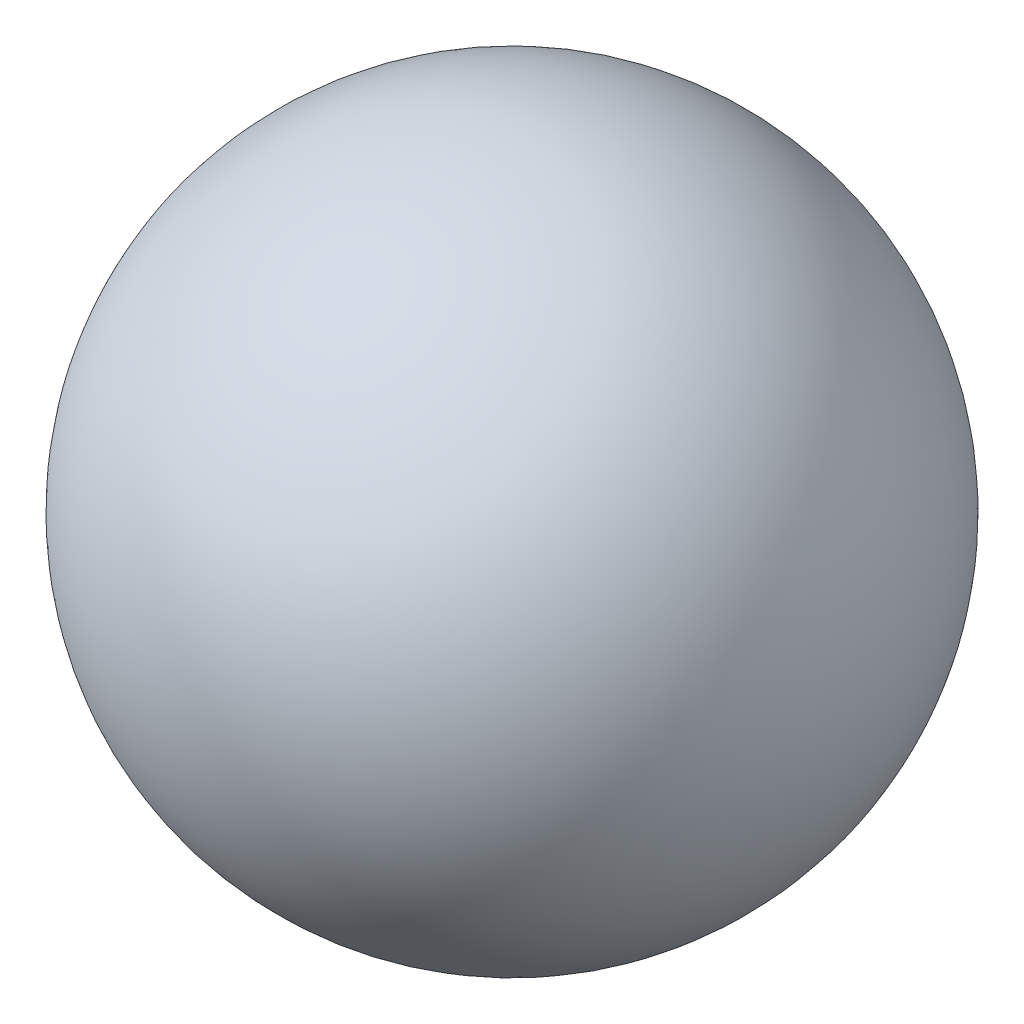
SolidWorks part; units mm, degrees
ref_plane "Front Plane" through (0, 0, 0) normal (0, 0, 1) x (1, 0, 0)
ref_plane "Top Plane" through (0, 0, 0) normal (0, 1, 0) x (1, 0, 0)
ref_plane "Right Plane" through (0, 0, 0) normal (1, 0, 0) x (0, 0, -1)
sketch "Sketch1" plane through (0, 0, 0) normal (0, 1, 0) x (1, 0, 0)
  line L0 (-12.0945, 0) -> (11.9055, 0)
  arc A0 (11.9055, 0) -> (-12.0945, 0) centre (-0.0945, 0) cw
  dimension "D1" = 24
revolve "Revolve1" add sketch "Sketch1" angle 360 about L0
